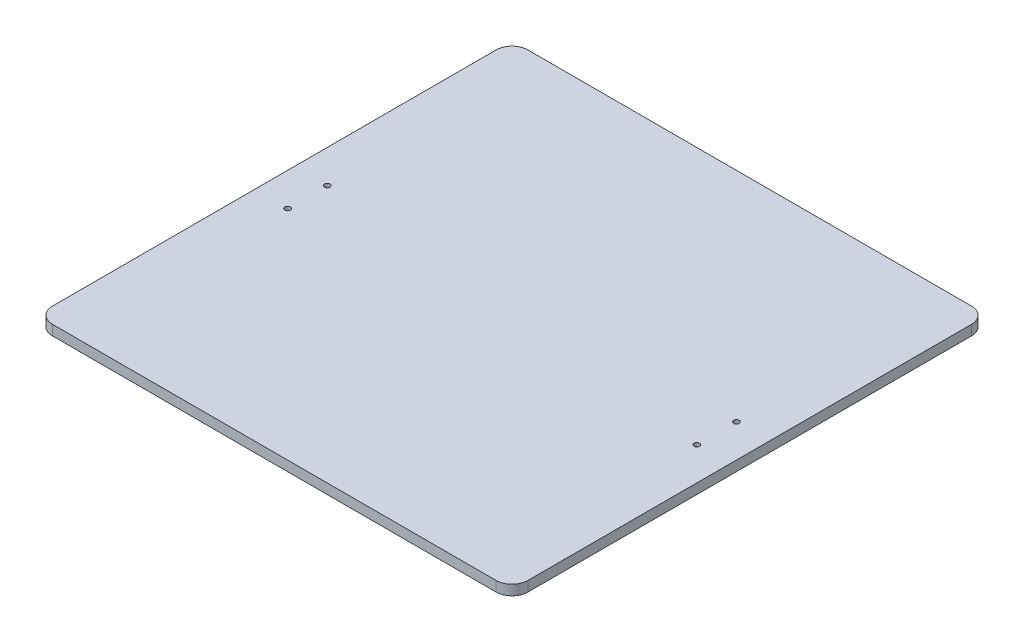
SolidWorks part; units mm, degrees
ref_plane "Front Plane" through (0, 0, 0) normal (0, 0, 1) x (1, 0, 0)
ref_plane "Top Plane" through (0, 0, 0) normal (0, 1, 0) x (1, 0, 0)
ref_plane "Right Plane" through (0, 0, 0) normal (1, 0, 0) x (0, 0, -1)
sketch "Sketch1" plane through (0, 0, 0) normal (0, 1, 0) x (1, 0, 0)
  line L1 (-150, 150) -> (150, 150)
  line L2 (-150, 150) -> (-150, -150)
  line L3 (-150, -150) -> (150, -150)
  line L4 (150, 150) -> (150, -150)
  line L5 (-150, 150) -> (150, -150) construction
  line L6 (-150, -150) -> (150, 150) construction
  point P0 (0, 0)
  dimension "D1" = 300
  dimension "D2" = 300
extrude "Boss-Extrude1" add sketch "Sketch1" along normal blind 6.35
fillet "Fillet1" radius 10 4 edges at (150, 3.175, -150) (150, 3.175, 150) (-150, 3.175, 150) (-150, 3.175, -150)
sketch "Sketch2" plane through (0, 6.35, 0) normal (0, 1, 0) x (1, 0, 0)
  line L0 (-150, 140) -> (-150, -140) construction
  line L1 (150, -140) -> (150, 140) construction
  line L2 (140, 150) -> (-140, 150) construction
  circle A0 centre (-129.12, 12.5) radius 1.75
  circle A1 centre (-129.12, -12.5) radius 1.75
  circle A2 centre (129.12, 12.5) radius 1.75
  circle A3 centre (129.12, -12.5) radius 1.75
  dimension "D1" = 3.5
  dimension "D2" = 3.5
  dimension "D3" = 3.5
  dimension "D4" = 3.5
  dimension "D5" = 20.88
  dimension "D6" = 20.88
  dimension "D7" = 20.88
  dimension "D8" = 20.88
  dimension "D9" = 137.5
  dimension "D10" = 137.5
  dimension "D11" = 25
  dimension "D12" = 25
extrude "Cut-Extrude1" cut sketch "Sketch2" against normal through all
